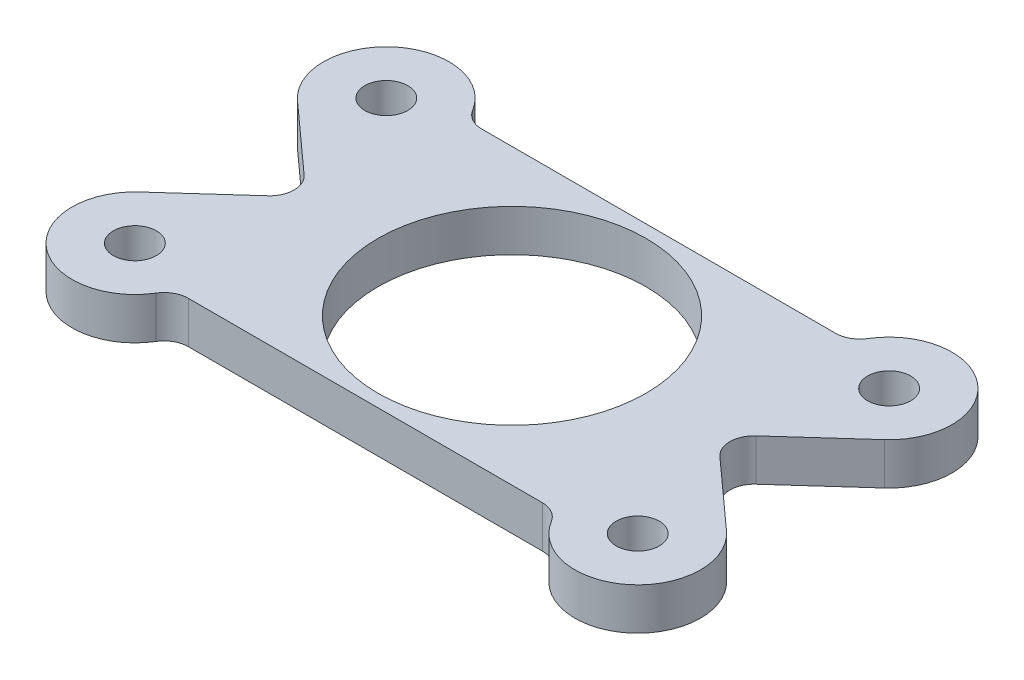
SolidWorks part; units mm, degrees
material "6061-T6 (SS)"
ref_plane "Front Plane" through (0, 0, 0) normal (0, 0, 1) x (1, 0, 0)
ref_plane "Top Plane" through (0, 0, 0) normal (0, 1, 0) x (1, 0, 0)
ref_plane "Right Plane" through (0, 0, 0) normal (1, 0, 0) x (0, 0, -1)
sketch "Sketch1" plane through (0, 0, 0) normal (0, 1, 0) x (1, 0, 0)
  line L0 (-22.2404, 5.989) -> (-17.1179, 1.3672)
  line L1 (-14.5599, 11.1125) -> (14.5599, 11.1125)
  line L2 (-17.1179, -1.3672) -> (-22.2404, -5.989)
  line L3 (-14.5599, -11.1125) -> (14.5599, -11.1125)
  line L4 (0, -1000) -> (0, 49000) construction
  line L5 (-25.4, 11.1125) -> (25.4, -11.1125) construction
  line L6 (-25.4, -11.1125) -> (25.4, 11.1125) construction
  line L7 (-19.05, 9.525) -> (19.05, 9.525) construction
  line L8 (-19.05, 9.525) -> (-19.05, -9.525) construction
  line L9 (-19.05, -9.525) -> (19.05, -9.525) construction
  line L10 (19.05, 9.525) -> (19.05, -9.525) construction
  line L11 (-19.05, 9.525) -> (19.05, -9.525) construction
  line L12 (-19.05, -9.525) -> (19.05, 9.525) construction
  line L13 (22.2404, 5.989) -> (17.1179, 1.3672)
  line L14 (17.1179, -1.3672) -> (22.2404, -5.989)
  circle A0 centre (0, 0) radius 10.16
  arc A1 (-22.2404, -5.989) -> (-14.5599, -11.1125) centre (-19.05, -9.525) ccw
  arc A2 (17.1179, -1.3672) -> (17.1179, 1.3672) centre (18.3515, 0) cw
  arc A4 (22.2404, 5.989) -> (14.5599, 11.1125) centre (19.05, 9.525) ccw
  arc A5 (-17.1179, -1.3672) -> (-17.1179, 1.3672) centre (-18.3515, 0) ccw
  arc A6 (-14.5599, 11.1125) -> (-22.2404, 5.989) centre (-19.05, 9.525) ccw
  arc A7 (14.5599, -11.1125) -> (22.2404, -5.989) centre (19.05, -9.525) ccw
  point P13 (-29.2717, 7.2996)
  point P14 (0, 0)
  point P29 (0, 0)
  point P30 (-35.3239, -11.1125)
  point P31 (0, 0)
  point P32 (0, 0)
  dimension "D1" = 20.32
  dimension "D6" = 9.525
  dimension "D7" = 3.683
  dimension "D8" = 6.35
  dimension "D2" = 22.225
  dimension "D3" = 50.8
  dimension "D4" = 38.1
  dimension "D5" = 19.05
extrude "Boss-Extrude1" add sketch "Sketch1" along normal blind 3.175
hole_wizard "#4 Clearance Hole1" positions "Sketch2" profile "Sketch3" hole size "#4" standard "ANSI Inch" end condition through all
sketch "Sketch2" plane through (0, 3.175, 0) normal (0, 1, 0) x (1, 0, 0)
  line L1 (19.05, -9.525) -> (-19.05, -9.525)
  line L2 (19.05, -9.525) -> (19.05, 9.525)
  line L3 (19.05, 9.525) -> (-19.05, 9.525)
  line L4 (-19.05, -9.525) -> (-19.05, 9.525)
  line L5 (19.05, -9.525) -> (-19.05, 9.525) construction
  line L6 (19.05, 9.525) -> (-19.05, -9.525) construction
  point P0 (-19.05, 9.525)
  point P2 (-19.05, -9.525)
  point P89 (19.05, -9.525)
  point P90 (19.05, 9.525)
  dimension "D1" = 19.05
  dimension "D2" = 38.1
sketch "Sketch3" plane through (-19.05, 3.175, -9.525) normal (1, 0, 0) x (0, 0, 1)
  line L0 (0, 0) -> (0, 3.175)
  line L1 (0, 3.175) -> (1.6319, 3.175)
  line L2 (1.6319, 3.175) -> (1.6319, 0)
  line L5 (1.6319, 0) -> (0, 0)
  line L11 (0, -6.35) -> (0, 107.95) construction
  dimension "Thru Hole Dia." = 3.2639
  dimension "Thru Hole Depth" = 3.175
fillet "Fillet1" radius 1.8415 4 edges at (-14.5599, 1.5875, 11.1125) (14.5599, 1.5875, 11.1125) (14.5599, 1.5875, -11.1125) (-14.5599, 1.5875, -11.1125)
